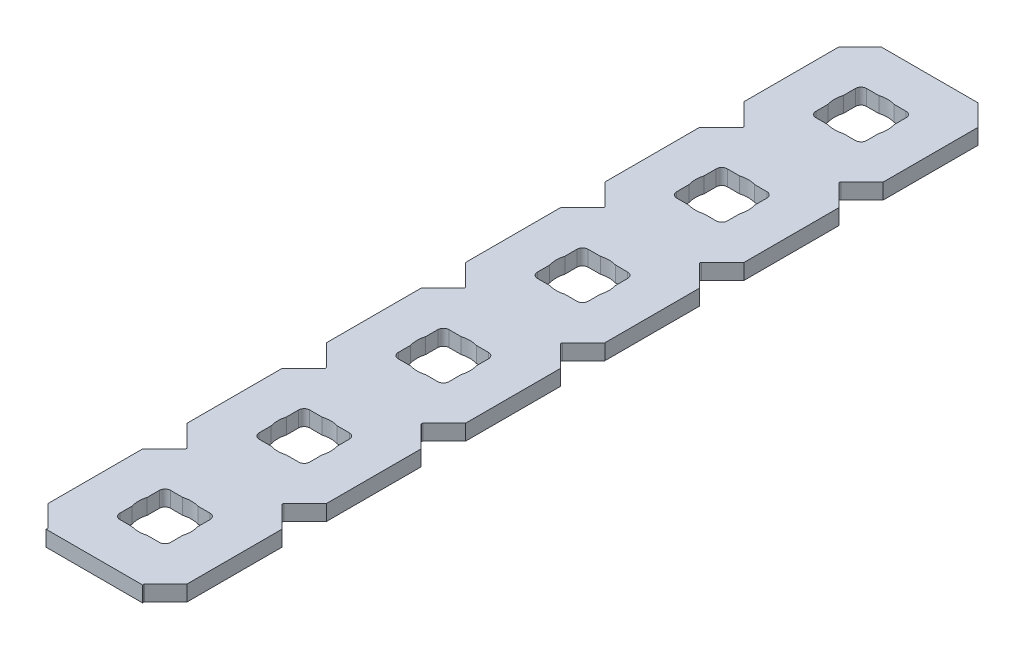
SolidWorks part; units mm, degrees
material "5052-H32"
ref_plane "Front Plane" through (0, 0, 0) normal (0, 0, 1) x (1, 0, 0)
ref_plane "Top Plane" through (0, 0, 0) normal (0, 1, 0) x (1, 0, 0)
ref_plane "Right Plane" through (0, 0, 0) normal (1, 0, 0) x (0, 0, -1)
ref_plane "Plane1" through (0, 0, 0) normal (0, -1, 0) x (1, 0, 0)
sketch "Sketch1" plane through (0, 0, 0) normal (0, -1, 0) x (1, 0, 0)
  line L0 (4.5466, -308.8386) -> (8.1534, -308.8386)
  line L1 (8.6614, -309.3466) -> (8.6614, -312.9534)
  line L2 (8.1534, -313.4614) -> (4.5466, -313.4614)
  line L3 (4.0386, -312.9534) -> (4.0386, -309.3466)
  line L4 (4.5466, -296.1386) -> (8.1534, -296.1386)
  line L5 (8.6614, -296.6466) -> (8.6614, -300.2534)
  line L6 (8.1534, -300.7614) -> (4.5466, -300.7614)
  line L7 (4.0386, -300.2534) -> (4.0386, -296.6466)
  line L8 (4.5466, -283.4386) -> (8.1534, -283.4386)
  line L9 (8.6614, -283.9466) -> (8.6614, -287.5534)
  line L10 (8.1534, -288.0614) -> (4.5466, -288.0614)
  line L11 (4.0386, -287.5534) -> (4.0386, -283.9466)
  line L12 (4.5466, -270.7386) -> (8.1534, -270.7386)
  line L13 (8.6614, -271.2466) -> (8.6614, -274.8534)
  line L14 (8.1534, -275.3614) -> (4.5466, -275.3614)
  line L15 (4.0386, -274.8534) -> (4.0386, -271.2466)
  line L16 (4.5466, -258.0386) -> (8.1534, -258.0386)
  line L17 (8.6614, -258.5466) -> (8.6614, -262.1534)
  line L18 (8.1534, -262.6614) -> (4.5466, -262.6614)
  line L19 (4.0386, -262.1534) -> (4.0386, -258.5466)
  line L20 (4.5466, -245.3386) -> (8.1534, -245.3386)
  line L21 (8.6614, -245.8466) -> (8.6614, -249.4534)
  line L22 (8.1534, -249.9614) -> (4.5466, -249.9614)
  line L23 (4.0386, -249.4534) -> (4.0386, -245.8466)
  line L24 (4.5466, -232.6386) -> (8.1534, -232.6386)
  line L25 (8.6614, -233.1466) -> (8.6614, -236.7534)
  line L26 (8.1534, -237.2614) -> (4.5466, -237.2614)
  line L27 (4.0386, -236.7534) -> (4.0386, -233.1466)
  line L28 (4.5466, -219.9386) -> (8.1534, -219.9386)
  line L29 (8.6614, -220.4466) -> (8.6614, -224.0534)
  line L30 (8.1534, -224.5614) -> (4.5466, -224.5614)
  line L31 (4.0386, -224.0534) -> (4.0386, -220.4466)
  line L32 (4.5466, -207.2386) -> (8.1534, -207.2386)
  line L33 (8.6614, -207.7466) -> (8.6614, -211.3534)
  line L34 (8.1534, -211.8614) -> (4.5466, -211.8614)
  line L35 (4.0386, -211.3534) -> (4.0386, -207.7466)
  line L36 (4.5466, -194.5386) -> (8.1534, -194.5386)
  line L37 (8.6614, -195.0466) -> (8.6614, -198.6534)
  line L38 (8.1534, -199.1614) -> (4.5466, -199.1614)
  line L39 (4.0386, -198.6534) -> (4.0386, -195.0466)
  line L40 (4.5466, -181.8386) -> (8.1534, -181.8386)
  line L41 (8.6614, -182.3466) -> (8.6614, -185.9534)
  line L42 (8.1534, -186.4614) -> (4.5466, -186.4614)
  line L43 (4.0386, -185.9534) -> (4.0386, -182.3466)
  line L44 (4.5466, -169.1386) -> (8.1534, -169.1386)
  line L45 (8.6614, -169.6466) -> (8.6614, -173.2534)
  line L46 (8.1534, -173.7614) -> (4.5466, -173.7614)
  line L47 (4.0386, -173.2534) -> (4.0386, -169.6466)
  line L48 (4.5466, -156.4386) -> (8.1534, -156.4386)
  line L49 (8.6614, -156.9466) -> (8.6614, -160.5534)
  line L50 (8.1534, -161.0614) -> (4.5466, -161.0614)
  line L51 (4.0386, -160.5534) -> (4.0386, -156.9466)
  line L52 (4.5466, -143.7386) -> (8.1534, -143.7386)
  line L53 (8.6614, -144.2466) -> (8.6614, -147.8534)
  line L54 (8.1534, -148.3614) -> (4.5466, -148.3614)
  line L55 (4.0386, -147.8534) -> (4.0386, -144.2466)
  line L56 (4.5466, -131.0386) -> (8.1534, -131.0386)
  line L57 (8.6614, -131.5466) -> (8.6614, -135.1534)
  line L58 (8.1534, -135.6614) -> (4.5466, -135.6614)
  line L59 (4.0386, -135.1534) -> (4.0386, -131.5466)
  line L60 (4.5466, -118.3386) -> (8.1534, -118.3386)
  line L61 (8.6614, -118.8466) -> (8.6614, -122.4534)
  line L62 (8.1534, -122.9614) -> (4.5466, -122.9614)
  line L63 (4.0386, -122.4534) -> (4.0386, -118.8466)
  line L64 (4.5466, -105.6386) -> (8.1534, -105.6386)
  line L65 (8.6614, -106.1466) -> (8.6614, -109.7534)
  line L66 (8.1534, -110.2614) -> (4.5466, -110.2614)
  line L67 (4.0386, -109.7534) -> (4.0386, -106.1466)
  line L68 (4.5466, -92.9386) -> (8.1534, -92.9386)
  line L69 (8.6614, -93.4466) -> (8.6614, -97.0534)
  line L70 (8.1534, -97.5614) -> (4.5466, -97.5614)
  line L71 (4.0386, -97.0534) -> (4.0386, -93.4466)
  line L72 (4.5466, -80.2386) -> (8.1534, -80.2386)
  line L73 (8.6614, -80.7466) -> (8.6614, -84.3534)
  line L74 (8.1534, -84.8614) -> (4.5466, -84.8614)
  line L75 (4.0386, -84.3534) -> (4.0386, -80.7466)
  line L76 (4.5466, -67.5386) -> (8.1534, -67.5386)
  line L77 (8.6614, -68.0466) -> (8.6614, -71.6534)
  line L78 (8.1534, -72.1614) -> (4.5466, -72.1614)
  line L79 (4.0386, -71.6534) -> (4.0386, -68.0466)
  line L80 (4.5466, -54.8386) -> (8.1534, -54.8386)
  line L81 (8.6614, -55.3466) -> (8.6614, -58.9534)
  line L82 (8.1534, -59.4614) -> (4.5466, -59.4614)
  line L83 (4.0386, -58.9534) -> (4.0386, -55.3466)
  line L84 (4.5466, -42.1386) -> (8.1534, -42.1386)
  line L85 (8.6614, -42.6466) -> (8.6614, -46.2534)
  line L86 (8.1534, -46.7614) -> (4.5466, -46.7614)
  line L87 (4.0386, -46.2534) -> (4.0386, -42.6466)
  line L88 (4.5466, -29.4386) -> (8.1534, -29.4386)
  line L89 (8.6614, -29.9466) -> (8.6614, -33.5534)
  line L90 (8.1534, -34.0614) -> (4.5466, -34.0614)
  line L91 (4.0386, -33.5534) -> (4.0386, -29.9466)
  line L92 (12.7, -302.773) -> (12.7, -294.127)
  line L93 (12.7, -294.127) -> (10.7628, -292.1898)
  line L94 (10.7628, -292.0102) -> (12.7, -290.073)
  line L95 (12.7, -290.073) -> (12.7, -281.427)
  line L96 (12.7, -281.427) -> (10.7628, -279.4898)
  line L97 (10.7628, -279.3102) -> (12.7, -277.373)
  line L98 (12.7, -277.373) -> (12.7, -268.727)
  line L99 (12.7, -268.727) -> (10.7628, -266.7898)
  line L100 (10.7628, -266.6102) -> (12.7, -264.673)
  line L101 (12.7, -264.673) -> (12.7, -256.027)
  line L102 (12.7, -256.027) -> (10.7628, -254.0898)
  line L103 (10.7628, -253.9102) -> (12.7, -251.973)
  line L104 (12.7, -251.973) -> (12.7, -243.327)
  line L105 (12.7, -243.327) -> (10.7628, -241.3898)
  line L106 (10.7628, -241.2102) -> (12.7, -239.273)
  line L107 (12.7, -239.273) -> (12.7, -230.627)
  line L108 (12.7, -230.627) -> (10.7628, -228.6898)
  line L109 (10.7628, -228.5102) -> (12.7, -226.573)
  line L110 (12.7, -226.573) -> (12.7, -217.927)
  line L111 (12.7, -217.927) -> (10.7628, -215.9898)
  line L112 (10.7628, -215.8102) -> (12.7, -213.873)
  line L113 (12.7, -213.873) -> (12.7, -205.227)
  line L114 (12.7, -205.227) -> (10.7628, -203.2898)
  line L115 (10.7628, -203.1102) -> (12.7, -201.173)
  line L116 (12.7, -201.173) -> (12.7, -192.527)
  line L117 (12.7, -192.527) -> (10.7628, -190.5898)
  line L118 (10.7628, -190.4102) -> (12.7, -188.473)
  line L119 (12.7, -188.473) -> (12.7, -179.827)
  line L120 (12.7, -179.827) -> (10.7628, -177.8898)
  line L121 (10.7628, -177.7102) -> (12.7, -175.773)
  line L122 (12.7, -175.773) -> (12.7, -167.127)
  line L123 (12.7, -167.127) -> (10.7628, -165.1898)
  line L124 (10.7628, -165.0102) -> (12.7, -163.073)
  line L125 (12.7, -163.073) -> (12.7, -154.427)
  line L126 (12.7, -154.427) -> (10.7628, -152.4898)
  line L127 (10.7628, -152.3102) -> (12.7, -150.373)
  line L128 (12.7, -150.373) -> (12.7, -141.727)
  line L129 (12.7, -141.727) -> (10.7628, -139.7898)
  line L130 (10.7628, -139.6102) -> (12.7, -137.673)
  line L131 (12.7, -137.673) -> (12.7, -129.027)
  line L132 (12.7, -129.027) -> (10.7628, -127.0898)
  line L133 (10.7628, -126.9102) -> (12.7, -124.973)
  line L134 (12.7, -124.973) -> (12.7, -116.327)
  line L135 (12.7, -116.327) -> (10.7628, -114.3898)
  line L136 (10.7628, -114.2102) -> (12.7, -112.273)
  line L137 (12.7, -112.273) -> (12.7, -103.627)
  line L138 (12.7, -103.627) -> (10.7628, -101.6898)
  line L139 (10.7628, -101.5102) -> (12.7, -99.573)
  line L140 (12.7, -99.573) -> (12.7, -90.927)
  line L141 (12.7, -90.927) -> (10.7628, -88.9898)
  line L142 (10.7628, -88.8102) -> (12.7, -86.873)
  line L143 (12.7, -86.873) -> (12.7, -78.227)
  line L144 (12.7, -78.227) -> (10.7628, -76.2898)
  line L145 (10.7628, -76.1102) -> (12.7, -74.173)
  line L146 (12.7, -74.173) -> (12.7, -65.527)
  line L147 (12.7, -65.527) -> (10.7628, -63.5898)
  line L148 (10.7628, -63.4102) -> (12.7, -61.473)
  line L149 (12.7, -61.473) -> (12.7, -52.827)
  line L150 (12.7, -52.827) -> (10.7628, -50.8898)
  line L151 (10.7628, -50.7102) -> (12.7, -48.773)
  line L152 (12.7, -48.773) -> (12.7, -40.127)
  line L153 (12.7, -40.127) -> (10.7628, -38.1898)
  line L154 (10.7628, -38.0102) -> (12.7, -36.073)
  line L155 (12.7, -36.073) -> (12.7, -27.427)
  line L156 (12.7, -27.427) -> (10.7628, -25.4898)
  line L157 (10.7628, -25.3102) -> (12.7, -23.373)
  line L158 (12.7, -23.373) -> (12.7, -14.727)
  line L159 (12.7, -14.727) -> (10.7628, -12.7898)
  line L160 (10.7628, -12.6102) -> (12.7, -10.673)
  line L161 (12.7, -10.673) -> (12.7, -2.032)
  line L162 (12.7, -2.032) -> (10.668, 0)
  line L163 (10.668, 0) -> (2.032, 0)
  line L164 (2.032, 0) -> (0, -2.032)
  line L165 (0, -2.032) -> (0, -10.673)
  line L166 (0, -10.673) -> (1.9372, -12.6102)
  line L167 (1.9372, -12.7898) -> (0, -14.727)
  line L168 (0, -14.727) -> (0, -23.373)
  line L169 (0, -23.373) -> (1.9372, -25.3102)
  line L170 (1.9372, -25.4898) -> (0, -27.427)
  line L171 (0, -27.427) -> (0, -36.073)
  line L172 (0, -36.073) -> (1.9372, -38.0102)
  line L173 (1.9372, -38.1898) -> (0, -40.127)
  line L174 (0, -40.127) -> (0, -48.773)
  line L175 (0, -48.773) -> (1.9372, -50.7102)
  line L176 (1.9372, -50.8898) -> (0, -52.827)
  line L177 (0, -52.827) -> (0, -61.473)
  line L178 (0, -61.473) -> (1.9372, -63.4102)
  line L179 (1.9372, -63.5898) -> (0, -65.527)
  line L180 (0, -65.527) -> (0, -74.173)
  line L181 (0, -74.173) -> (1.9372, -76.1102)
  line L182 (1.9372, -76.2898) -> (0, -78.227)
  line L183 (0, -78.227) -> (0, -86.873)
  line L184 (0, -86.873) -> (1.9372, -88.8102)
  line L185 (1.9372, -88.9898) -> (0, -90.927)
  line L186 (0, -90.927) -> (0, -99.573)
  line L187 (0, -99.573) -> (1.9372, -101.5102)
  line L188 (1.9372, -101.6898) -> (0, -103.627)
  line L189 (0, -103.627) -> (0, -112.273)
  line L190 (0, -112.273) -> (1.9372, -114.2102)
  line L191 (1.9372, -114.3898) -> (0, -116.327)
  line L192 (0, -116.327) -> (0, -124.973)
  line L193 (0, -124.973) -> (1.9372, -126.9102)
  line L194 (1.9372, -127.0898) -> (0, -129.027)
  line L195 (0, -129.027) -> (0, -137.673)
  line L196 (0, -137.673) -> (1.9372, -139.6102)
  line L197 (1.9372, -139.7898) -> (0, -141.727)
  line L198 (0, -141.727) -> (0, -150.373)
  line L199 (0, -150.373) -> (1.9372, -152.3102)
  line L200 (1.9372, -152.4898) -> (0, -154.427)
  line L201 (0, -154.427) -> (0, -163.073)
  line L202 (0, -163.073) -> (1.9372, -165.0102)
  line L203 (1.9372, -165.1898) -> (0, -167.127)
  line L204 (0, -167.127) -> (0, -175.773)
  line L205 (0, -175.773) -> (1.9372, -177.7102)
  line L206 (1.9372, -177.8898) -> (0, -179.827)
  line L207 (0, -179.827) -> (0, -188.473)
  line L208 (0, -188.473) -> (1.9372, -190.4102)
  line L209 (1.9372, -190.5898) -> (0, -192.527)
  line L210 (0, -192.527) -> (0, -201.173)
  line L211 (0, -201.173) -> (1.9372, -203.1102)
  line L212 (1.9372, -203.2898) -> (0, -205.227)
  line L213 (0, -205.227) -> (0, -213.873)
  line L214 (0, -213.873) -> (1.9372, -215.8102)
  line L215 (1.9372, -215.9898) -> (0, -217.927)
  line L216 (0, -217.927) -> (0, -226.573)
  line L217 (0, -226.573) -> (1.9372, -228.5102)
  line L218 (1.9372, -228.6898) -> (0, -230.627)
  line L219 (0, -230.627) -> (0, -239.273)
  line L220 (0, -239.273) -> (1.9372, -241.2102)
  line L221 (1.9372, -241.3898) -> (0, -243.327)
  line L222 (0, -243.327) -> (0, -251.973)
  line L223 (0, -251.973) -> (1.9372, -253.9102)
  line L224 (1.9372, -254.0898) -> (0, -256.027)
  line L225 (0, -256.027) -> (0, -264.673)
  line L226 (0, -264.673) -> (1.9372, -266.6102)
  line L227 (1.9372, -266.7898) -> (0, -268.727)
  line L228 (0, -268.727) -> (0, -277.373)
  line L229 (0, -277.373) -> (1.9372, -279.3102)
  line L230 (1.9372, -279.4898) -> (0, -281.427)
  line L231 (0, -281.427) -> (0, -290.073)
  line L232 (0, -290.073) -> (1.9372, -292.0102)
  line L233 (1.9372, -292.1898) -> (0, -294.127)
  line L234 (0, -294.127) -> (0, -302.773)
  line L235 (0, -302.773) -> (1.9372, -304.7102)
  line L236 (1.9372, -304.8898) -> (0, -306.827)
  line L237 (0, -306.827) -> (0, -315.468)
  line L238 (0, -315.468) -> (2.032, -317.5)
  line L239 (2.032, -317.5) -> (10.668, -317.5)
  line L240 (10.668, -317.5) -> (12.7, -315.468)
  line L241 (12.7, -315.468) -> (12.7, -306.827)
  line L242 (12.7, -306.827) -> (10.7628, -304.8898)
  line L243 (10.7628, -304.7102) -> (12.7, -302.773)
  line L244 (8.1534, -8.6614) -> (4.5466, -8.6614)
  line L245 (4.0386, -8.1534) -> (4.0386, -4.5466)
  line L246 (4.5466, -4.0386) -> (8.1534, -4.0386)
  line L247 (8.6614, -4.5466) -> (8.6614, -8.1534)
  line L248 (4.0386, -20.8534) -> (4.0386, -17.2466)
  line L249 (4.5466, -16.7386) -> (8.1534, -16.7386)
  line L250 (8.6614, -17.2466) -> (8.6614, -20.8534)
  line L251 (8.1534, -21.3614) -> (4.5466, -21.3614)
  arc A0 (4.0386, -309.3466) -> (4.5466, -308.8386) centre (4.5466, -309.3466) cw
  arc A1 (8.1534, -308.8386) -> (8.6614, -309.3466) centre (8.1534, -309.3466) cw
  arc A2 (8.6614, -312.9534) -> (8.1534, -313.4614) centre (8.1534, -312.9534) cw
  arc A3 (4.5466, -313.4614) -> (4.0386, -312.9534) centre (4.5466, -312.9534) cw
  arc A4 (4.0386, -296.6466) -> (4.5466, -296.1386) centre (4.5466, -296.6466) cw
  arc A5 (8.1534, -296.1386) -> (8.6614, -296.6466) centre (8.1534, -296.6466) cw
  arc A6 (8.6614, -300.2534) -> (8.1534, -300.7614) centre (8.1534, -300.2534) cw
  arc A7 (4.5466, -300.7614) -> (4.0386, -300.2534) centre (4.5466, -300.2534) cw
  arc A8 (4.0386, -283.9466) -> (4.5466, -283.4386) centre (4.5466, -283.9466) cw
  arc A9 (8.1534, -283.4386) -> (8.6614, -283.9466) centre (8.1534, -283.9466) cw
  arc A10 (8.6614, -287.5534) -> (8.1534, -288.0614) centre (8.1534, -287.5534) cw
  arc A11 (4.5466, -288.0614) -> (4.0386, -287.5534) centre (4.5466, -287.5534) cw
  arc A12 (4.0386, -271.2466) -> (4.5466, -270.7386) centre (4.5466, -271.2466) cw
  arc A13 (8.1534, -270.7386) -> (8.6614, -271.2466) centre (8.1534, -271.2466) cw
  arc A14 (8.6614, -274.8534) -> (8.1534, -275.3614) centre (8.1534, -274.8534) cw
  arc A15 (4.5466, -275.3614) -> (4.0386, -274.8534) centre (4.5466, -274.8534) cw
  arc A16 (4.0386, -258.5466) -> (4.5466, -258.0386) centre (4.5466, -258.5466) cw
  arc A17 (8.1534, -258.0386) -> (8.6614, -258.5466) centre (8.1534, -258.5466) cw
  arc A18 (8.6614, -262.1534) -> (8.1534, -262.6614) centre (8.1534, -262.1534) cw
  arc A19 (4.5466, -262.6614) -> (4.0386, -262.1534) centre (4.5466, -262.1534) cw
  arc A20 (4.0386, -245.8466) -> (4.5466, -245.3386) centre (4.5466, -245.8466) cw
  arc A21 (8.1534, -245.3386) -> (8.6614, -245.8466) centre (8.1534, -245.8466) cw
  arc A22 (8.6614, -249.4534) -> (8.1534, -249.9614) centre (8.1534, -249.4534) cw
  arc A23 (4.5466, -249.9614) -> (4.0386, -249.4534) centre (4.5466, -249.4534) cw
  arc A24 (4.0386, -233.1466) -> (4.5466, -232.6386) centre (4.5466, -233.1466) cw
  arc A25 (8.1534, -232.6386) -> (8.6614, -233.1466) centre (8.1534, -233.1466) cw
  arc A26 (8.6614, -236.7534) -> (8.1534, -237.2614) centre (8.1534, -236.7534) cw
  arc A27 (4.5466, -237.2614) -> (4.0386, -236.7534) centre (4.5466, -236.7534) cw
  arc A28 (4.0386, -220.4466) -> (4.5466, -219.9386) centre (4.5466, -220.4466) cw
  arc A29 (8.1534, -219.9386) -> (8.6614, -220.4466) centre (8.1534, -220.4466) cw
  arc A30 (8.6614, -224.0534) -> (8.1534, -224.5614) centre (8.1534, -224.0534) cw
  arc A31 (4.5466, -224.5614) -> (4.0386, -224.0534) centre (4.5466, -224.0534) cw
  arc A32 (4.0386, -207.7466) -> (4.5466, -207.2386) centre (4.5466, -207.7466) cw
  arc A33 (8.1534, -207.2386) -> (8.6614, -207.7466) centre (8.1534, -207.7466) cw
  arc A34 (8.6614, -211.3534) -> (8.1534, -211.8614) centre (8.1534, -211.3534) cw
  arc A35 (4.5466, -211.8614) -> (4.0386, -211.3534) centre (4.5466, -211.3534) cw
  arc A36 (4.0386, -195.0466) -> (4.5466, -194.5386) centre (4.5466, -195.0466) cw
  arc A37 (8.1534, -194.5386) -> (8.6614, -195.0466) centre (8.1534, -195.0466) cw
  arc A38 (8.6614, -198.6534) -> (8.1534, -199.1614) centre (8.1534, -198.6534) cw
  arc A39 (4.5466, -199.1614) -> (4.0386, -198.6534) centre (4.5466, -198.6534) cw
  arc A40 (4.0386, -182.3466) -> (4.5466, -181.8386) centre (4.5466, -182.3466) cw
  arc A41 (8.1534, -181.8386) -> (8.6614, -182.3466) centre (8.1534, -182.3466) cw
  arc A42 (8.6614, -185.9534) -> (8.1534, -186.4614) centre (8.1534, -185.9534) cw
  arc A43 (4.5466, -186.4614) -> (4.0386, -185.9534) centre (4.5466, -185.9534) cw
  arc A44 (4.0386, -169.6466) -> (4.5466, -169.1386) centre (4.5466, -169.6466) cw
  arc A45 (8.1534, -169.1386) -> (8.6614, -169.6466) centre (8.1534, -169.6466) cw
  arc A46 (8.6614, -173.2534) -> (8.1534, -173.7614) centre (8.1534, -173.2534) cw
  arc A47 (4.5466, -173.7614) -> (4.0386, -173.2534) centre (4.5466, -173.2534) cw
  arc A48 (4.0386, -156.9466) -> (4.5466, -156.4386) centre (4.5466, -156.9466) cw
  arc A49 (8.1534, -156.4386) -> (8.6614, -156.9466) centre (8.1534, -156.9466) cw
  arc A50 (8.6614, -160.5534) -> (8.1534, -161.0614) centre (8.1534, -160.5534) cw
  arc A51 (4.5466, -161.0614) -> (4.0386, -160.5534) centre (4.5466, -160.5534) cw
  arc A52 (4.0386, -144.2466) -> (4.5466, -143.7386) centre (4.5466, -144.2466) cw
  arc A53 (8.1534, -143.7386) -> (8.6614, -144.2466) centre (8.1534, -144.2466) cw
  arc A54 (8.6614, -147.8534) -> (8.1534, -148.3614) centre (8.1534, -147.8534) cw
  arc A55 (4.5466, -148.3614) -> (4.0386, -147.8534) centre (4.5466, -147.8534) cw
  arc A56 (4.0386, -131.5466) -> (4.5466, -131.0386) centre (4.5466, -131.5466) cw
  arc A57 (8.1534, -131.0386) -> (8.6614, -131.5466) centre (8.1534, -131.5466) cw
  arc A58 (8.6614, -135.1534) -> (8.1534, -135.6614) centre (8.1534, -135.1534) cw
  arc A59 (4.5466, -135.6614) -> (4.0386, -135.1534) centre (4.5466, -135.1534) cw
  arc A60 (4.0386, -118.8466) -> (4.5466, -118.3386) centre (4.5466, -118.8466) cw
  arc A61 (8.1534, -118.3386) -> (8.6614, -118.8466) centre (8.1534, -118.8466) cw
  arc A62 (8.6614, -122.4534) -> (8.1534, -122.9614) centre (8.1534, -122.4534) cw
  arc A63 (4.5466, -122.9614) -> (4.0386, -122.4534) centre (4.5466, -122.4534) cw
  arc A64 (4.0386, -106.1466) -> (4.5466, -105.6386) centre (4.5466, -106.1466) cw
  arc A65 (8.1534, -105.6386) -> (8.6614, -106.1466) centre (8.1534, -106.1466) cw
  arc A66 (8.6614, -109.7534) -> (8.1534, -110.2614) centre (8.1534, -109.7534) cw
  arc A67 (4.5466, -110.2614) -> (4.0386, -109.7534) centre (4.5466, -109.7534) cw
  arc A68 (4.0386, -93.4466) -> (4.5466, -92.9386) centre (4.5466, -93.4466) cw
  arc A69 (8.1534, -92.9386) -> (8.6614, -93.4466) centre (8.1534, -93.4466) cw
  arc A70 (8.6614, -97.0534) -> (8.1534, -97.5614) centre (8.1534, -97.0534) cw
  arc A71 (4.5466, -97.5614) -> (4.0386, -97.0534) centre (4.5466, -97.0534) cw
  arc A72 (4.0386, -80.7466) -> (4.5466, -80.2386) centre (4.5466, -80.7466) cw
  arc A73 (8.1534, -80.2386) -> (8.6614, -80.7466) centre (8.1534, -80.7466) cw
  arc A74 (8.6614, -84.3534) -> (8.1534, -84.8614) centre (8.1534, -84.3534) cw
  arc A75 (4.5466, -84.8614) -> (4.0386, -84.3534) centre (4.5466, -84.3534) cw
  arc A76 (4.0386, -68.0466) -> (4.5466, -67.5386) centre (4.5466, -68.0466) cw
  arc A77 (8.1534, -67.5386) -> (8.6614, -68.0466) centre (8.1534, -68.0466) cw
  arc A78 (8.6614, -71.6534) -> (8.1534, -72.1614) centre (8.1534, -71.6534) cw
  arc A79 (4.5466, -72.1614) -> (4.0386, -71.6534) centre (4.5466, -71.6534) cw
  arc A80 (4.0386, -55.3466) -> (4.5466, -54.8386) centre (4.5466, -55.3466) cw
  arc A81 (8.1534, -54.8386) -> (8.6614, -55.3466) centre (8.1534, -55.3466) cw
  arc A82 (8.6614, -58.9534) -> (8.1534, -59.4614) centre (8.1534, -58.9534) cw
  arc A83 (4.5466, -59.4614) -> (4.0386, -58.9534) centre (4.5466, -58.9534) cw
  arc A84 (4.0386, -42.6466) -> (4.5466, -42.1386) centre (4.5466, -42.6466) cw
  arc A85 (8.1534, -42.1386) -> (8.6614, -42.6466) centre (8.1534, -42.6466) cw
  arc A86 (8.6614, -46.2534) -> (8.1534, -46.7614) centre (8.1534, -46.2534) cw
  arc A87 (4.5466, -46.7614) -> (4.0386, -46.2534) centre (4.5466, -46.2534) cw
  arc A88 (4.0386, -29.9466) -> (4.5466, -29.4386) centre (4.5466, -29.9466) cw
  arc A89 (8.1534, -29.4386) -> (8.6614, -29.9466) centre (8.1534, -29.9466) cw
  arc A90 (8.6614, -33.5534) -> (8.1534, -34.0614) centre (8.1534, -33.5534) cw
  arc A91 (4.5466, -34.0614) -> (4.0386, -33.5534) centre (4.5466, -33.5534) cw
  arc A92 (10.7628, -292.1898) -> (10.7628, -292.0102) centre (10.8526, -292.1) cw
  arc A93 (10.7628, -279.4898) -> (10.7628, -279.3102) centre (10.8526, -279.4) cw
  arc A94 (10.7628, -266.7898) -> (10.7628, -266.6102) centre (10.8526, -266.7) cw
  arc A95 (10.7628, -254.0898) -> (10.7628, -253.9102) centre (10.8526, -254) cw
  arc A96 (10.7628, -241.3898) -> (10.7628, -241.2102) centre (10.8526, -241.3) cw
  arc A97 (10.7628, -228.6898) -> (10.7628, -228.5102) centre (10.8526, -228.6) cw
  arc A98 (10.7628, -215.9898) -> (10.7628, -215.8102) centre (10.8526, -215.9) cw
  arc A99 (10.7628, -203.2898) -> (10.7628, -203.1102) centre (10.8526, -203.2) cw
  arc A100 (10.7628, -190.5898) -> (10.7628, -190.4102) centre (10.8526, -190.5) cw
  arc A101 (10.7628, -177.8898) -> (10.7628, -177.7102) centre (10.8526, -177.8) cw
  arc A102 (10.7628, -165.1898) -> (10.7628, -165.0102) centre (10.8526, -165.1) cw
  arc A103 (10.7628, -152.4898) -> (10.7628, -152.3102) centre (10.8526, -152.4) cw
  arc A104 (10.7628, -139.7898) -> (10.7628, -139.6102) centre (10.8526, -139.7) cw
  arc A105 (10.7628, -127.0898) -> (10.7628, -126.9102) centre (10.8526, -127) cw
  arc A106 (10.7628, -114.3898) -> (10.7628, -114.2102) centre (10.8526, -114.3) cw
  arc A107 (10.7628, -101.6898) -> (10.7628, -101.5102) centre (10.8526, -101.6) cw
  arc A108 (10.7628, -88.9898) -> (10.7628, -88.8102) centre (10.8526, -88.9) cw
  arc A109 (10.7628, -76.2898) -> (10.7628, -76.1102) centre (10.8526, -76.2) cw
  arc A110 (10.7628, -63.5898) -> (10.7628, -63.4102) centre (10.8526, -63.5) cw
  arc A111 (10.7628, -50.8898) -> (10.7628, -50.7102) centre (10.8526, -50.8) cw
  arc A112 (10.7628, -38.1898) -> (10.7628, -38.0102) centre (10.8526, -38.1) cw
  arc A113 (10.7628, -25.4898) -> (10.7628, -25.3102) centre (10.8526, -25.4) cw
  arc A114 (10.7628, -12.7898) -> (10.7628, -12.6102) centre (10.8526, -12.7) cw
  arc A115 (1.9372, -12.6102) -> (1.9372, -12.7898) centre (1.8474, -12.7) cw
  arc A116 (1.9372, -25.3102) -> (1.9372, -25.4898) centre (1.8474, -25.4) cw
  arc A117 (1.9372, -38.0102) -> (1.9372, -38.1898) centre (1.8474, -38.1) cw
  arc A118 (1.9372, -50.7102) -> (1.9372, -50.8898) centre (1.8474, -50.8) cw
  arc A119 (1.9372, -63.4102) -> (1.9372, -63.5898) centre (1.8474, -63.5) cw
  arc A120 (1.9372, -76.1102) -> (1.9372, -76.2898) centre (1.8474, -76.2) cw
  arc A121 (1.9372, -88.8102) -> (1.9372, -88.9898) centre (1.8474, -88.9) cw
  arc A122 (1.9372, -101.5102) -> (1.9372, -101.6898) centre (1.8474, -101.6) cw
  arc A123 (1.9372, -114.2102) -> (1.9372, -114.3898) centre (1.8474, -114.3) cw
  arc A124 (1.9372, -126.9102) -> (1.9372, -127.0898) centre (1.8474, -127) cw
  arc A125 (1.9372, -139.6102) -> (1.9372, -139.7898) centre (1.8474, -139.7) cw
  arc A126 (1.9372, -152.3102) -> (1.9372, -152.4898) centre (1.8474, -152.4) cw
  arc A127 (1.9372, -165.0102) -> (1.9372, -165.1898) centre (1.8474, -165.1) cw
  arc A128 (1.9372, -177.7102) -> (1.9372, -177.8898) centre (1.8474, -177.8) cw
  arc A129 (1.9372, -190.4102) -> (1.9372, -190.5898) centre (1.8474, -190.5) cw
  arc A130 (1.9372, -203.1102) -> (1.9372, -203.2898) centre (1.8474, -203.2) cw
  arc A131 (1.9372, -215.8102) -> (1.9372, -215.9898) centre (1.8474, -215.9) cw
  arc A132 (1.9372, -228.5102) -> (1.9372, -228.6898) centre (1.8474, -228.6) cw
  arc A133 (1.9372, -241.2102) -> (1.9372, -241.3898) centre (1.8474, -241.3) cw
  arc A134 (1.9372, -253.9102) -> (1.9372, -254.0898) centre (1.8474, -254) cw
  arc A135 (1.9372, -266.6102) -> (1.9372, -266.7898) centre (1.8474, -266.7) cw
  arc A136 (1.9372, -279.3102) -> (1.9372, -279.4898) centre (1.8474, -279.4) cw
  arc A137 (1.9372, -292.0102) -> (1.9372, -292.1898) centre (1.8474, -292.1) cw
  arc A138 (1.9372, -304.7102) -> (1.9372, -304.8898) centre (1.8474, -304.8) cw
  arc A139 (10.7628, -304.8898) -> (10.7628, -304.7102) centre (10.8526, -304.8) cw
  arc A140 (8.6614, -8.1534) -> (8.1534, -8.6614) centre (8.1534, -8.1534) cw
  arc A141 (4.5466, -8.6614) -> (4.0386, -8.1534) centre (4.5466, -8.1534) cw
  arc A142 (4.0386, -4.5466) -> (4.5466, -4.0386) centre (4.5466, -4.5466) cw
  arc A143 (8.1534, -4.0386) -> (8.6614, -4.5466) centre (8.1534, -4.5466) cw
  arc A144 (4.0386, -17.2466) -> (4.5466, -16.7386) centre (4.5466, -17.2466) cw
  arc A145 (8.1534, -16.7386) -> (8.6614, -17.2466) centre (8.1534, -17.2466) cw
  arc A146 (8.6614, -20.8534) -> (8.1534, -21.3614) centre (8.1534, -20.8534) cw
  arc A147 (4.5466, -21.3614) -> (4.0386, -20.8534) centre (4.5466, -20.8534) cw
extrude "Boss-Extrude1" add sketch "Sketch1" against normal blind 1.4224
sketch "Sketch2" plane through (0, 1.4224, 0) normal (0, 1, 0) x (1, 0, 0)
  line L0 (6.35, 4.0386) -> (6.35, 8.6614) construction
  line L1 (8.1534, 4.0386) -> (4.5466, 4.0386) construction
  line L2 (4.5466, 8.6614) -> (8.1534, 8.6614) construction
  circle A0 centre (6.35, 6.35) radius 2.413
  dimension "D1" = 4.826
extrude "Cut-Extrude1" cut sketch "Sketch2" against normal blind 2.54
pattern_linear "LPattern1" count 25 spacing 12.7 along (0, 0, -1) of "Cut-Extrude1"
sketch "Sketch3" plane through (0, 1.4224, 0) normal (0, 1, 0) x (1, 0, 0)
  line L0 (0, 256.027) -> (0, 264.673) construction
  line L1 (0, 317.5) -> (12.7, 317.5)
  line L2 (0, 317.5) -> (0, 253.9102)
  line L3 (0, 253.9102) -> (12.7, 253.9102)
  line L4 (12.7, 317.5) -> (12.7, 253.9102)
  line L5 (12.7, 264.673) -> (12.7, 256.027) construction
  line L6 (2.032, 317.5) -> (10.668, 317.5) construction
extrude "Cut-Extrude2" cut sketch "Sketch3" against normal through all
sketch "Sketch4" plane through (0, 1.4224, 0) normal (0, 1, 0) x (1, 0, 0)
  line L1 (-7.2618, 177.7102) -> (23.8983, 177.7102)
  line L2 (-7.2618, 177.7102) -> (-7.2618, -7.9455)
  line L3 (-7.2618, -7.9455) -> (23.8983, -7.9455)
  line L4 (23.8983, 177.7102) -> (23.8983, -7.9455)
extrude "Cut-Extrude3" cut sketch "Sketch4" against normal blind 2.54
